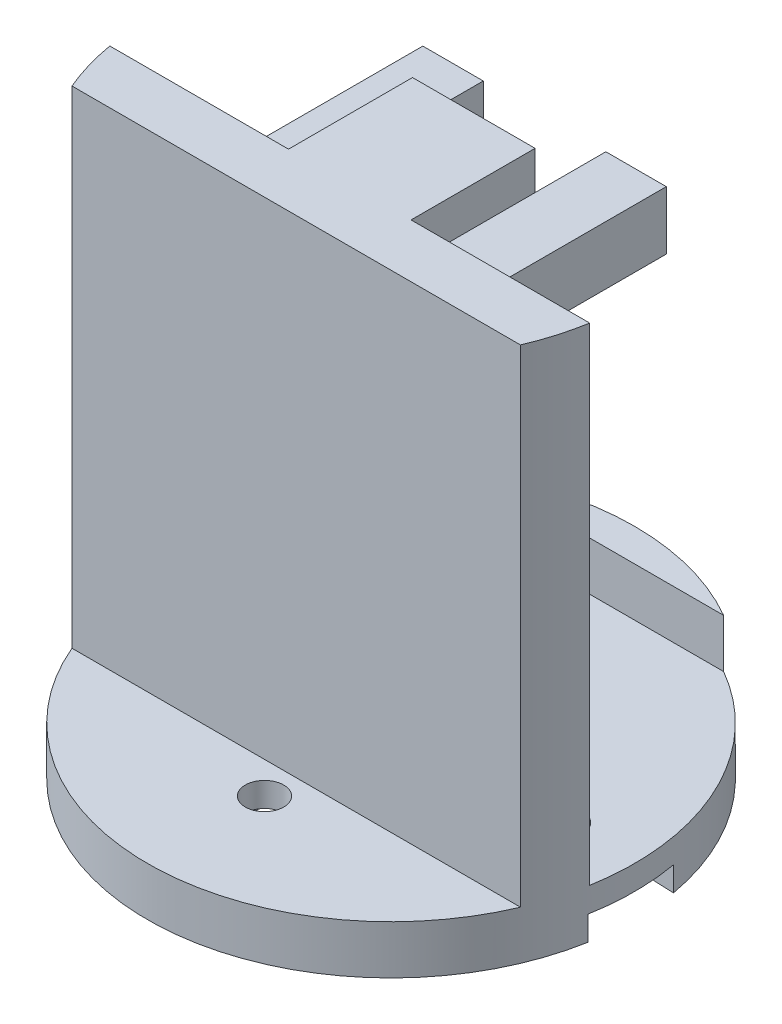
SolidWorks part; units mm, degrees
ref_plane "Front Plane" through (0, 0, 0) normal (0, 0, 1) x (1, 0, 0)
ref_plane "Top Plane" through (0, 0, 0) normal (0, 1, 0) x (1, 0, 0)
ref_plane "Right Plane" through (0, 0, 0) normal (1, 0, 0) x (0, 0, -1)
sketch "Sketch1" plane through (0, 0, 0) normal (0, 1, 0) x (1, 0, 0)
  circle A0 centre (0, 0) radius 12.7
  dimension "D1" = 25.4
extrude "Boss-Extrude1" add sketch "Sketch1" along normal blind 2.54
sketch "Sketch2" plane through (0, 2.54, 0) normal (0, 1, 0) x (1, 0, 0)
  line L0 (12.5165, -2.1512) -> (-12.5165, -2.1512)
  line L1 (0, 0) -> (0, -12.7) construction
  line L3 (11.6976, -4.9452) -> (-11.6976, -4.9452)
  arc A0 (-12.5165, -2.1512) -> (-11.6976, -4.9452) centre (0, 0) ccw
  circle A1 centre (0, 0) radius 12.7 construction
  arc A2 (11.6976, -4.9452) -> (12.5165, -2.1512) centre (0, 0) ccw
  dimension "D1" = 2.1512
  dimension "D2" = 2.794
extrude "Boss-Extrude2" add sketch "Sketch2" along normal blind 25.4
ref_plane "Plane1" through (0, 0, -12.7) normal (0, 0, -1) x (-1, 0, 0)
ref_plane "Plane2" through (0, 0, -4.318) normal (0, 0, -1) x (-1, 0, 0)
sketch "Sketch3" plane through (0, 0, -4.318) normal (0, 0, -1) x (-1, 0, 0)
  line L0 (-12.5165, 27.94) -> (12.5165, 27.94) construction
  line L1 (-3.197, 21.5461) -> (3.197, 21.5461)
  line L2 (-3.197, 21.5461) -> (-3.197, 27.94)
  line L3 (-3.197, 27.94) -> (3.197, 27.94)
  line L4 (3.197, 21.5461) -> (3.197, 27.94)
  line L5 (-3.197, 21.5461) -> (3.197, 27.94) construction
  line L6 (-3.197, 27.94) -> (3.197, 21.5461) construction
  line L7 (-12.5165, 9.6507) -> (12.5165, 9.6507) construction
  line L8 (-12.5165, 27.94) -> (-12.5165, 2.54) construction
  line L9 (12.5165, 27.94) -> (12.5165, 2.54) construction
  point P0 (0, 24.743)
  point P7 (0, 9.6507)
  dimension "D1" = 6.3939
extrude "Boss-Extrude3" add sketch "Sketch3" against normal up to next
sketch "Sketch4" plane through (0, 0, -4.318) normal (0, 0, -1) x (-1, 0, 0)
  line L0 (-3.197, 27.94) -> (3.197, 21.5461) construction
  line L1 (3.197, 27.94) -> (-2.562, 22.1811) construction
  circle A0 centre (0, 24.743) radius 1.397
  dimension "D1" = 2.794
extrude "Cut-Extrude1" cut sketch "Sketch4" against normal blind 5.588
ref_plane "Plane3" through (0, 0, 12.7) normal (0, 0, 1) x (1, 0, 0)
sketch "Sketch6" plane through (0, 0, 0) normal (0, -1, 0) x (1, 0, 0)
  line L0 (6.8, 0) -> (50006.8, 0) construction
  line L1 (0, 0) -> (0, -50000) construction
  circle A0 centre (9, 0) radius 1
  circle A1 centre (0, 6.6) radius 0.6 construction
  circle A3 centre (0, -6.6) radius 1
  circle A4 centre (-9, 0) radius 1
  circle A5 centre (0, 6.6) radius 1
  circle A6 centre (0, 0) radius 1
  circle A8 centre (0, -6.6) radius 0.6 construction
  circle A9 centre (-9, 0) radius 0.675 construction
  circle A10 centre (9, 0) radius 0.675 construction
  point P19 (0, 0)
  dimension "D1" = 2
  dimension "D3" = 2
extrude "Cut-Extrude2" cut sketch "Sketch6" against normal up to next
sketch "Sketch9" plane through (0, 0, 0) normal (0, -1, 0) x (1, 0, 0)
  line L0 (-2, -6.6) -> (-2, -2.9933)
  line L1 (-2, -6.6) -> (-2, -2.9933) construction
  line L2 (-2.5904, -2.5) -> (-3.6, -2.5)
  line L3 (-2.5904, -2.5) -> (-3.6, -2.5) construction
  line L4 (-3.6, -2.5) -> (-15.6, -2)
  line L5 (-3.6, -2.5) -> (-15.6, -2) construction
  line L6 (-15.6, 2) -> (-3.6, 2.5)
  line L7 (-15.6, 2) -> (-3.6, 2.5) construction
  line L8 (-3.6, 2.5) -> (-2.5904, 2.5)
  line L9 (-3.6, 2.5) -> (-2.5904, 2.5) construction
  line L10 (-2, 2.9933) -> (-2, 6.6)
  line L11 (-2, 2.9933) -> (-2, 6.6) construction
  line L12 (2, 6.6) -> (2, 2.9933)
  line L13 (2, 6.6) -> (2, 2.9933) construction
  line L14 (2.5904, 2.5) -> (3.6, 2.5)
  line L15 (2.5904, 2.5) -> (3.6, 2.5) construction
  line L16 (3.6, 2.5) -> (15.6, 2)
  line L17 (3.6, 2.5) -> (15.6, 2) construction
  line L18 (15.6, -2) -> (3.6, -2.5)
  line L19 (15.6, -2) -> (3.6, -2.5) construction
  line L20 (3.6, -2.5) -> (2.5904, -2.5)
  line L21 (3.6, -2.5) -> (2.5904, -2.5) construction
  line L22 (2, -2.9933) -> (2, -6.6)
  line L23 (2, -2.9933) -> (2, -6.6) construction
  line L24 (-2.1, -6.6) -> (-2.1, -3.0463)
  line L25 (-2.6325, -2.6) -> (-3.6021, -2.6)
  line L26 (-3.6021, -2.6) -> (-15.6021, -2.1)
  line L27 (-15.6021, 2.1) -> (-3.6021, 2.6)
  line L28 (-3.6021, 2.6) -> (-2.6325, 2.6)
  line L29 (-2.1, 3.0463) -> (-2.1, 6.6)
  line L30 (2.1, 6.6) -> (2.1, 3.0463)
  line L31 (2.6325, 2.6) -> (3.6021, 2.6)
  line L32 (3.6021, 2.6) -> (15.6021, 2.1)
  line L33 (15.6021, -2.1) -> (3.6021, -2.6)
  line L34 (3.6021, -2.6) -> (2.6325, -2.6)
  line L35 (2.1, -3.0463) -> (2.1, -6.6)
  arc A0 (-2.5904, -2.5) -> (-2, -2.9933) centre (0, 0) ccw
  arc A1 (-2.5904, -2.5) -> (-2, -2.9933) centre (0, 0) ccw construction
  arc A2 (-15.6, 2) -> (-15.6, -2) centre (-15.6, 0) ccw
  arc A3 (-15.6, 2) -> (-15.6, -2) centre (-15.6, 0) ccw construction
  arc A4 (-2, 2.9933) -> (-2.5904, 2.5) centre (0, 0) ccw
  arc A5 (-2, 2.9933) -> (-2.5904, 2.5) centre (0, 0) ccw construction
  arc A6 (2, 6.6) -> (-2, 6.6) centre (0, 6.6) ccw
  arc A7 (2, 6.6) -> (-2, 6.6) centre (0, 6.6) ccw construction
  arc A8 (2.5904, 2.5) -> (2, 2.9933) centre (0, 0) ccw
  arc A9 (2.5904, 2.5) -> (2, 2.9933) centre (0, 0) ccw construction
  arc A10 (15.6, -2) -> (15.6, 2) centre (15.6, 0) ccw
  arc A11 (15.6, -2) -> (15.6, 2) centre (15.6, 0) ccw construction
  arc A12 (2, -2.9933) -> (2.5904, -2.5) centre (0, 0) ccw
  arc A13 (2, -2.9933) -> (2.5904, -2.5) centre (0, 0) ccw construction
  arc A14 (-2, -6.6) -> (2, -6.6) centre (0, -6.6) ccw
  arc A15 (-2, -6.6) -> (2, -6.6) centre (0, -6.6) ccw construction
  arc A16 (-2.6325, -2.6) -> (-2.1, -3.0463) centre (0, 0) ccw
  arc A17 (-15.6021, 2.1) -> (-15.6021, -2.1) centre (-15.6, 0) ccw
  arc A18 (-2.1, 3.0463) -> (-2.6325, 2.6) centre (0, 0) ccw
  arc A19 (2.1, 6.6) -> (-2.1, 6.6) centre (0, 6.6) ccw
  arc A20 (2.6325, 2.6) -> (2.1, 3.0463) centre (0, 0) ccw
  arc A21 (15.6021, -2.1) -> (15.6021, 2.1) centre (15.6, 0) ccw
  arc A22 (2.1, -3.0463) -> (2.6325, -2.6) centre (0, 0) ccw
  arc A23 (-2.1, -6.6) -> (2.1, -6.6) centre (0, -6.6) ccw
  dimension "D1" = 0.1
extrude "Cut-Extrude4" cut sketch "Sketch9" against normal blind 1.27
sketch "Sketch10" plane through (0, 0, 2.1512) normal (0, 0, -1) x (-1, 0, 0)
  line L0 (-12.5165, 27.94) -> (-3.197, 27.94) construction
  line L1 (-6.35, 25.94) -> (6.35, 25.94)
  line L2 (-6.35, 25.94) -> (-6.35, 22.892)
  line L3 (-6.35, 22.892) -> (6.35, 22.892)
  line L4 (6.35, 25.94) -> (6.35, 22.892)
  line L5 (-6.35, 25.94) -> (6.35, 22.892) construction
  line L6 (-6.35, 22.892) -> (6.35, 25.94) construction
  line L11 (3.197, 21.5461) -> (3.197, 27.94)
  line L12 (3.197, 27.94) -> (-3.197, 27.94)
  line L13 (-3.197, 27.94) -> (-3.197, 21.5461)
  line L14 (-3.197, 21.5461) -> (3.197, 21.5461)
  line L15 (3.197, 21.5461) -> (3.197, 27.94)
  line L16 (3.197, 27.94) -> (-3.197, 27.94)
  line L17 (-3.197, 27.94) -> (-3.197, 21.5461)
  line L18 (-3.197, 21.5461) -> (3.197, 21.5461)
  point P0 (0, 24.416)
  point P7 (0, 0)
  point P10 (0, 25.94)
  point P12 (0, 27.94)
  line M10 (3.197, 27.94) -> (3.197, 21.5461)
  line M12 (-3.197, 21.5461) -> (-3.197, 27.94)
  dimension "D1" = 3.048
  dimension "D2" = 2
  dimension ".5" = 12.7
  dimension "D3" = 0
extrude "Boss-Extrude4" add sketch "Sketch10" along normal blind 10.16 contours L2 L3 L1 M12 | L4 L1 L3 M10
chamfer "Chamfer1" distance 1.27 angle 45 3 edges at (-4.7735, 22.892, 2.1512) (0, 21.5461, 2.1512) (4.7735, 22.892, 2.1512)
sketch "Sketch11" plane through (0, 2.54, 0) normal (0, 1, 0) x (1, 0, 0)
  line L0 (-6.35, 10.9985) -> (6.35, 10.9985)
  line L1 (-3.197, -2.1512) -> (-12.5165, -2.1512) construction
  arc A0 (6.35, 10.9985) -> (-6.35, 10.9985) centre (0, 0) ccw
  arc A1 (12.5165, -2.1512) -> (-12.5165, -2.1512) centre (0, 0) ccw construction
  dimension "D1" = 12.7
extrude "Boss-Extrude5" add sketch "Sketch11" along normal blind 2.54
